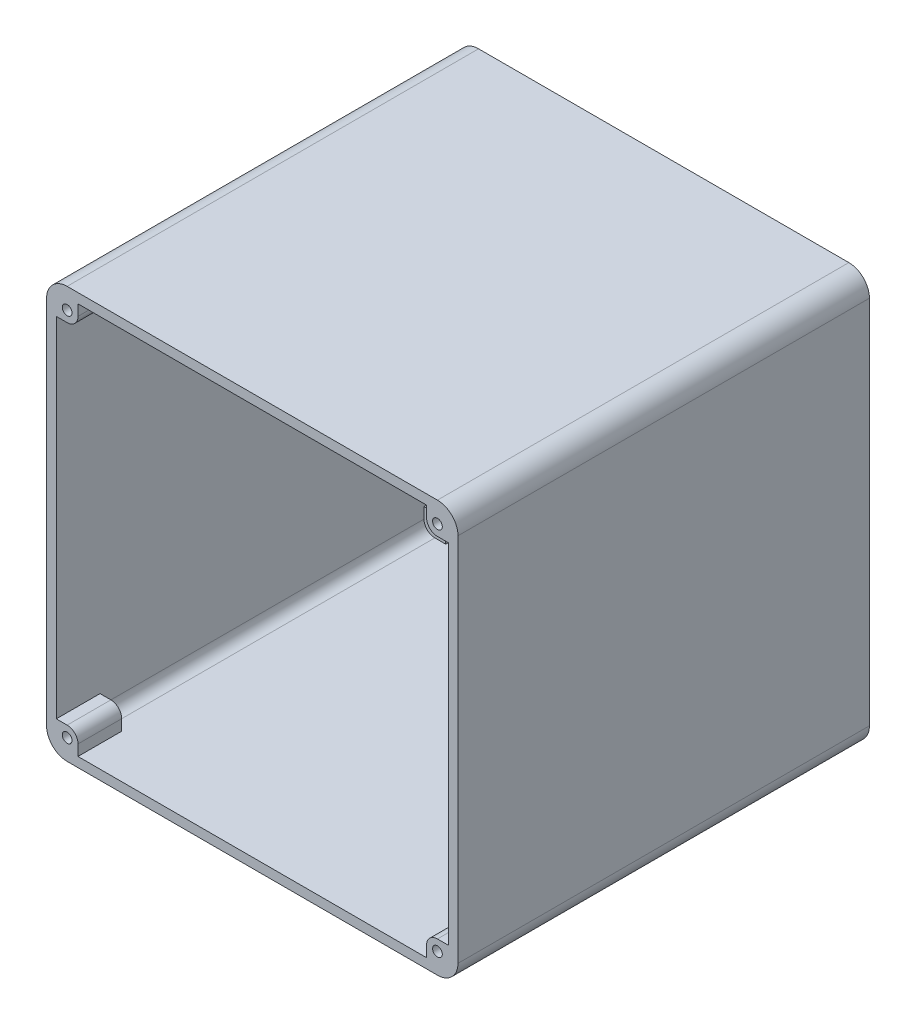
SolidWorks part; units mm, degrees
ref_plane "Front Plane" through (0, 0, 0) normal (0, 0, 1) x (1, 0, 0)
ref_plane "Top Plane" through (0, 0, 0) normal (0, 1, 0) x (1, 0, 0)
ref_plane "Right Plane" through (0, 0, 0) normal (1, 0, 0) x (0, 0, -1)
sketch "Sketch1" plane through (0, 0, 0) normal (0, 0, 1) x (1, 0, 0)
  line L1 (-63.5, -63.5) -> (-63.5, 63.5)
  line L2 (-60.5, -60.5) -> (60.5, -60.5)
  line L3 (-60.5, -60.5) -> (-60.5, 60.5)
  line L4 (-60.5, 60.5) -> (60.5, 60.5)
  line L5 (60.5, -60.5) -> (60.5, 60.5)
  line L6 (-60.5, -60.5) -> (60.5, 60.5) construction
  line L7 (-60.5, 60.5) -> (60.5, -60.5) construction
  line L8 (-63.5, 63.5) -> (63.5, 63.5)
  line L9 (63.5, -63.5) -> (63.5, 63.5)
  line L10 (-63.5, -63.5) -> (63.5, -63.5)
  circle A0 centre (0, 0) radius 44.45 construction
  circle A1 centre (0, 0) radius 38.5
  circle A2 centre (0, 0) radius 60.5 construction
  dimension "D1" = 88.9
  dimension "D2" = 77
  dimension "D3" = 121
  dimension "D4" = 3
extrude "Boss-Extrude1" add sketch "Sketch1" along normal blind 13.5 contours L1 L10 L9 L8 L5 L2 L3 L4 | L2 L5 L4 L3 A1 | A1
fillet "Fillet1" radius 6.35 4 edges at (63.5, 63.5, 6.75) (63.5, -63.5, 6.75) (-63.5, -63.5, 6.75) (-63.5, 63.5, 6.75)
sketch "Sketch2" plane through (0, 0, 13.5) normal (0, 0, 1) x (1, 0, 0)
  line L0 (-60.5, 0) -> (60.5, 0) construction
  line L1 (0, -60.5) -> (0, 60.5) construction
  line L2 (53.8, 57.15) -> (53.8, 60.5)
  line L3 (57.15, 53.8) -> (60.5, 53.8)
  line L4 (-53.8, 57.15) -> (-53.8, 60.5)
  line L5 (-57.15, 53.8) -> (-60.5, 53.8)
  line L6 (60.5, 53.8) -> (60.5, -53.8)
  line L7 (57.15, -53.8) -> (60.5, -53.8)
  line L8 (60.5, -57.15) -> (60.5, 57.15)
  line L9 (57.15, 60.5) -> (-57.15, 60.5)
  line L10 (-60.5, 57.15) -> (-60.5, -57.15)
  line L11 (-57.15, -60.5) -> (57.15, -60.5)
  line L13 (53.8, 60.5) -> (-53.8, 60.5)
  line L14 (-60.5, 53.8) -> (-60.5, -53.8)
  line L15 (53.8, -57.15) -> (53.8, -60.5)
  line L16 (-53.8, -57.15) -> (-53.8, -60.5)
  line L17 (-57.15, -53.8) -> (-60.5, -53.8)
  line L18 (53.8, -60.5) -> (-53.8, -60.5)
  circle A0 centre (57.15, 57.15) radius 1.5
  arc A1 (57.15, 53.8) -> (53.8, 57.15) centre (57.15, 57.15) cw
  circle A2 centre (57.15, -57.15) radius 1.5
  arc A3 (57.15, -53.8) -> (53.8, -57.15) centre (57.15, -57.15) ccw
  circle A4 centre (-57.15, 57.15) radius 1.5
  arc A5 (-57.15, 53.8) -> (-53.8, 57.15) centre (-57.15, 57.15) ccw
  circle A6 centre (-57.15, -57.15) radius 1.5
  arc A7 (-57.15, -53.8) -> (-53.8, -57.15) centre (-57.15, -57.15) cw
  arc A8 (60.5, 57.15) -> (57.15, 60.5) centre (57.15, 57.15) ccw
  arc A9 (-57.15, 60.5) -> (-60.5, 57.15) centre (-57.15, 57.15) ccw
  arc A10 (-60.5, -57.15) -> (-57.15, -60.5) centre (-57.15, -57.15) ccw
  arc A11 (57.15, -60.5) -> (60.5, -57.15) centre (57.15, -57.15) ccw
  point P16 (0, 60.5)
  point P23 (-224.2187, 73.6449)
  point P24 (-316.3429, 55.5656)
  point P28 (60.5, 0)
  point P39 (-60.5, 0)
  dimension "D2" = 3
  dimension "D1" = 3
extrude "Cut-Extrude1" cut sketch "Sketch2" against normal through all
sketch "Sketch3" plane through (0, 0, 13.5) normal (0, 0, 1) x (1, 0, 0)
  line L19 (-57.15, -60.5) -> (57.15, -60.5)
  line L20 (-60.5, 57.15) -> (-60.5, -57.15)
  line L21 (57.15, 60.5) -> (-57.15, 60.5)
  line L22 (60.5, -57.15) -> (60.5, 57.15)
  line L23 (-57.15, -60.5) -> (57.15, -60.5)
  line L24 (-60.5, 57.15) -> (-60.5, -57.15)
  line L25 (57.15, 60.5) -> (-57.15, 60.5)
  line L26 (60.5, -57.15) -> (60.5, 57.15)
  arc A19 (57.15, -60.5) -> (60.5, -57.15) centre (57.15, -57.15) ccw
  arc A20 (-60.5, -57.15) -> (-57.15, -60.5) centre (-57.15, -57.15) ccw
  arc A21 (-57.15, 60.5) -> (-60.5, 57.15) centre (-57.15, 57.15) ccw
  arc A22 (60.5, 57.15) -> (57.15, 60.5) centre (57.15, 57.15) ccw
  arc A23 (57.15, -60.5) -> (60.5, -57.15) centre (57.15, -57.15) ccw
  arc A24 (-60.5, -57.15) -> (-57.15, -60.5) centre (-57.15, -57.15) ccw
  arc A25 (-57.15, 60.5) -> (-60.5, 57.15) centre (-57.15, 57.15) ccw
  arc A26 (60.5, 57.15) -> (57.15, 60.5) centre (57.15, 57.15) ccw
  dimension "D1" = 3
sketch "Sketch4" plane through (0, 0, 0) normal (0, 0, -1) x (-1, 0, 0)
  line L8 (57.15, 60.5) -> (-57.15, 60.5)
  line L9 (60.5, -57.15) -> (60.5, 57.15)
  line L10 (-57.15, -60.5) -> (57.15, -60.5)
  line L11 (-60.5, 57.15) -> (-60.5, -57.15)
  line L12 (57.15, 60.5) -> (-57.15, 60.5)
  line L13 (60.5, -57.15) -> (60.5, 57.15)
  line L14 (-57.15, -60.5) -> (57.15, -60.5)
  line L15 (-60.5, 57.15) -> (-60.5, -57.15)
  arc A9 (60.5, 57.15) -> (57.15, 60.5) centre (57.15, 57.15) ccw
  arc A10 (57.15, -60.5) -> (60.5, -57.15) centre (57.15, -57.15) ccw
  arc A11 (-60.5, -57.15) -> (-57.15, -60.5) centre (-57.15, -57.15) ccw
  arc A12 (-57.15, 60.5) -> (-60.5, 57.15) centre (-57.15, 57.15) ccw
  arc A13 (60.5, 57.15) -> (57.15, 60.5) centre (57.15, 57.15) ccw
  arc A14 (57.15, -60.5) -> (60.5, -57.15) centre (57.15, -57.15) ccw
  arc A15 (-60.5, -57.15) -> (-57.15, -60.5) centre (-57.15, -57.15) ccw
  arc A16 (-57.15, 60.5) -> (-60.5, 57.15) centre (-57.15, 57.15) ccw
  line M13 (60.5, 53.8) -> (60.5, -53.8)
  line M17 (53.8, -60.5) -> (-53.8, -60.5)
  line M21 (-60.5, -53.8) -> (-60.5, 53.8)
  line M25 (-53.8, 60.5) -> (53.8, 60.5)
  line M29 (57.15, 63.5) -> (-57.15, 63.5)
  arc M30 (-57.15, 63.5) -> (-63.5, 57.15) centre (-57.15, 57.15) ccw
  line M31 (-63.5, 57.15) -> (-63.5, -57.15)
  arc M32 (-63.5, -57.15) -> (-57.15, -63.5) centre (-57.15, -57.15) ccw
  line M33 (-57.15, -63.5) -> (57.15, -63.5)
  arc M34 (57.15, -63.5) -> (63.5, -57.15) centre (57.15, -57.15) ccw
  line M35 (63.5, -57.15) -> (63.5, 57.15)
  arc M36 (63.5, 57.15) -> (57.15, 63.5) centre (57.15, 57.15) ccw
  dimension "D1" = 3
extrude "Boss-Extrude2" add sketch "Sketch4" along normal blind 100 contours A16 L12 A13 L13 A14 L14 A15 L15 M36 M29 M30 M31 M32 M33 M34 M35 M25 M13 M17 M21
sketch "Sketch5" plane through (0, 0, -100) normal (0, 0, -1) x (-1, 0, 0)
  line L0 (-53.8, 60.5) -> (-53.8, 57.15)
  line L1 (-57.15, 53.8) -> (-60.5, 53.8)
  line L2 (-15.0638, 0) -> (15.0638, 0) construction
  line L3 (0, 15.0638) -> (0, -15.0638) construction
  line L4 (53.8, 60.5) -> (53.8, 57.15)
  line L5 (57.15, 53.8) -> (60.5, 53.8)
  line L6 (57.15, -53.8) -> (60.5, -53.8)
  line L7 (53.8, -60.5) -> (53.8, -57.15)
  line L8 (-57.15, -53.8) -> (-60.5, -53.8)
  line L9 (-53.8, -60.5) -> (-53.8, -57.15)
  circle A0 centre (-57.15, 57.15) radius 1.5
  circle A1 centre (-57.15, 57.15) radius 1.5 construction
  arc A2 (-53.8, 57.15) -> (-57.15, 53.8) centre (-57.15, 57.15) cw
  circle A3 centre (57.15, 57.15) radius 1.5
  arc A4 (53.8, 57.15) -> (57.15, 53.8) centre (57.15, 57.15) ccw
  arc A5 (53.8, -57.15) -> (57.15, -53.8) centre (57.15, -57.15) cw
  circle A6 centre (57.15, -57.15) radius 1.5
  arc A7 (-53.8, -57.15) -> (-57.15, -53.8) centre (-57.15, -57.15) ccw
  circle A8 centre (-57.15, -57.15) radius 1.5
  point P18 (0, 0)
  point P22 (0, 0)
  arc M1 (-60.5, 57.15) -> (-57.15, 60.5) centre (-57.15, 57.15) cw
  line M2 (-57.15, 60.5) -> (57.15, 60.5)
  arc M3 (57.15, 60.5) -> (60.5, 57.15) centre (57.15, 57.15) cw
  line M4 (60.5, 57.15) -> (60.5, -57.15)
  arc M5 (60.5, -57.15) -> (57.15, -60.5) centre (57.15, -57.15) cw
  line M6 (57.15, -60.5) -> (-57.15, -60.5)
  arc M7 (-57.15, -60.5) -> (-60.5, -57.15) centre (-57.15, -57.15) cw
  line M8 (-60.5, -57.15) -> (-60.5, 57.15)
  arc M9 (63.5, 57.15) -> (57.15, 63.5) centre (57.15, 57.15) ccw
  line M10 (57.15, 63.5) -> (-57.15, 63.5)
  arc M11 (-57.15, 63.5) -> (-63.5, 57.15) centre (-57.15, 57.15) ccw
  line M12 (-63.5, 57.15) -> (-63.5, -57.15)
  arc M13 (-63.5, -57.15) -> (-57.15, -63.5) centre (-57.15, -57.15) ccw
  line M14 (-57.15, -63.5) -> (57.15, -63.5)
  arc M15 (57.15, -63.5) -> (63.5, -57.15) centre (57.15, -57.15) ccw
  line M16 (63.5, -57.15) -> (63.5, 57.15)
  dimension "D1" = 3
extrude "Boss-Extrude3" add sketch "Sketch5" along normal blind 13.5 contours A2 L0 L1 A0 M2 M1 M8 | L4 A4 L5 A3 M4 M3 M2 | A5 L7 L6 A6 M6 M5 M4 | L9 A7 L8 A8 M8 M7 M6 | M16 M9 M10 M11 M12 M13 M14 M15 M8 M1 M2 M3 M4 M5 M6 M7
